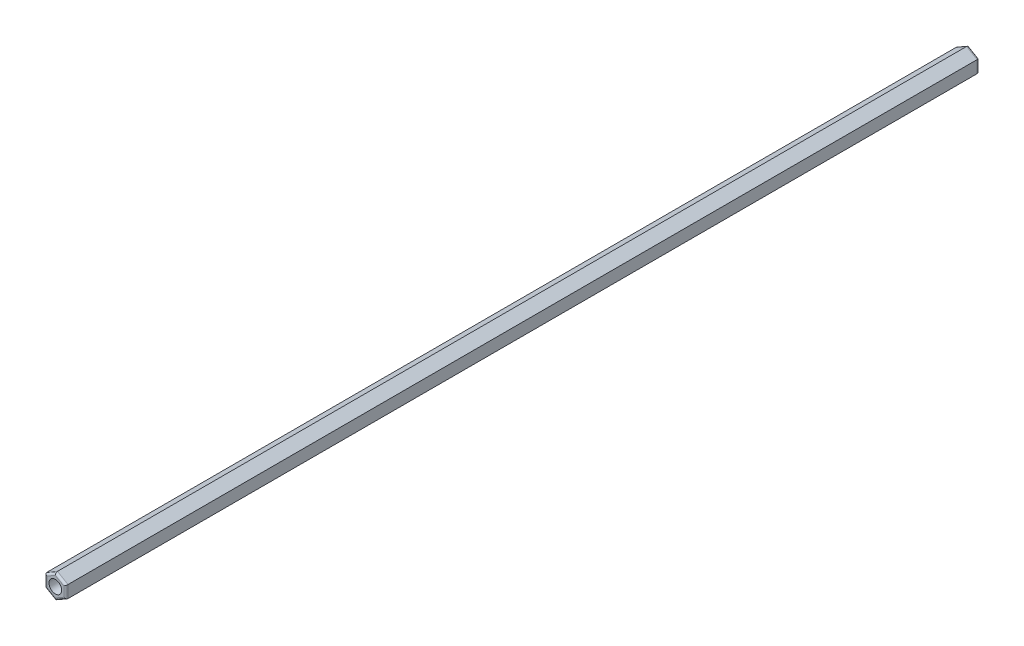
SolidWorks part; units mm, degrees
material "Inox rev"
ref_plane "Plano frontal" through (0, 0, 0) normal (0, 0, 1) x (1, 0, 0)
ref_plane "Plano superior" through (0, 0, 0) normal (0, 1, 0) x (1, 0, 0)
ref_plane "Plano direito" through (0, 0, 0) normal (1, 0, 0) x (0, 0, -1)
ref_plane "Plano1" through (0, 0, 0) normal (0, 0, -1) x (-1, 0, 0)
sketch "Esboço1" plane through (0, 0, 0) normal (0, 0, -1) x (-1, 0, 0)
  line L0 (67.5021, -1.4434) -> (70.0021, -2.8868)
  line L1 (70.0021, -2.8868) -> (72.5021, -1.4434)
  line L2 (72.5021, -1.4434) -> (72.5021, 1.4434)
  line L3 (72.5021, 1.4434) -> (70.0021, 2.8868)
  line L4 (70.0021, 2.8868) -> (67.5021, 1.4434)
  line L5 (67.5021, 1.4434) -> (67.5021, -1.4434)
extrude "Ressalto-extrusão1" add sketch "Esboço1" against normal blind 216
fillet "Filete1" radius 0.5 12 edges at (-71.2521, 2.1651, 0) (-72.5021, 0, 0) (-68.7521, 2.1651, 0) (-71.2521, -2.1651, 0) (-67.5021, 0, 0) (-68.7521, -2.1651, 0) (-71.2521, 2.1651, 216) (-72.5021, 0, 216) (-68.7521, 2.1651, 216) (-71.2521, -2.1651, 216) (-67.5021, 0, 216) (-68.7521, -2.1651, 216)
sketch "Esboço2" plane through (0, 0, 216) normal (0, 0, 1) x (1, 0, 0)
  circle A0 centre (-70.0021, 0) radius 1.5
  dimension "D1" = 3
extrude "Corte-extrusão1" cut sketch "Esboço2" against normal through all
